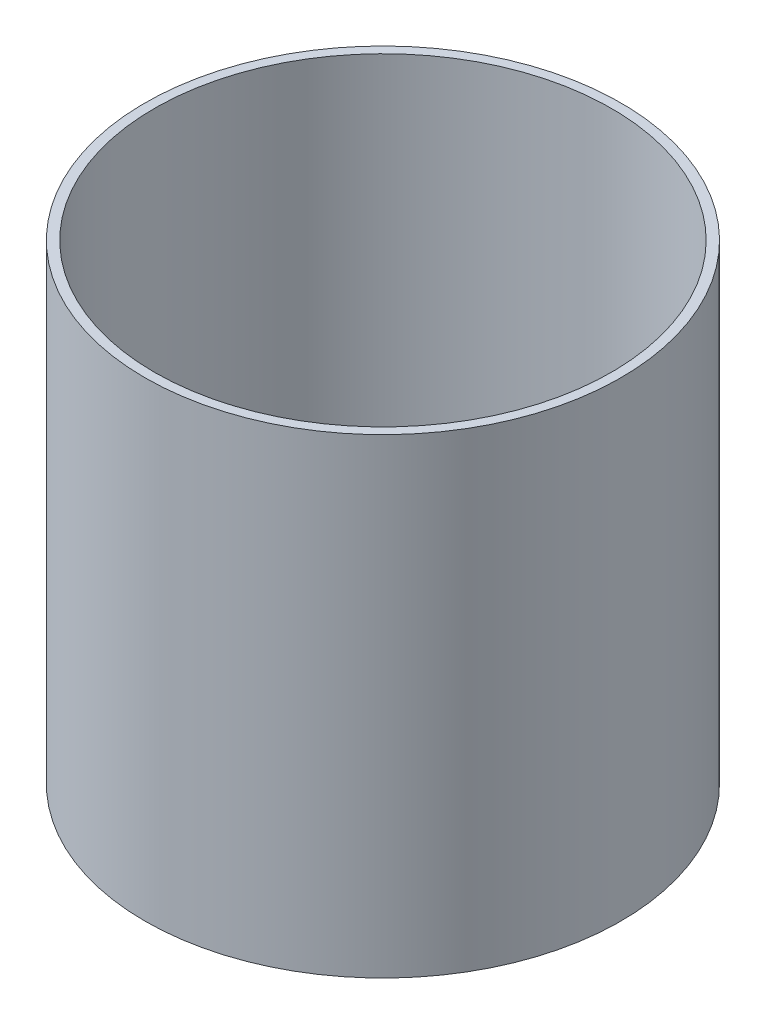
SolidWorks part; units mm, degrees
ref_plane "Front Plane" through (0, 0, 0) normal (0, 0, 1) x (1, 0, 0)
ref_plane "Top Plane" through (0, 0, 0) normal (0, 1, 0) x (1, 0, 0)
ref_plane "Right Plane" through (0, 0, 0) normal (1, 0, 0) x (0, 0, -1)
sketch "Sketch2" plane through (0, 0, 0) normal (0, 1, 0) x (1, 0, 0)
  circle A0 centre (0, 0) radius 57.15
extrude "Boss-Extrude3" add sketch "Sketch2" along normal blind 113 contours A0
sketch "Sketch8" plane through (0, 113, 0) normal (0, 1, 0) x (1, 0, 0)
  circle A0 centre (0, 0) radius 54.8815
extrude "Cut-Extrude1" cut sketch "Sketch8" against normal blind 109
